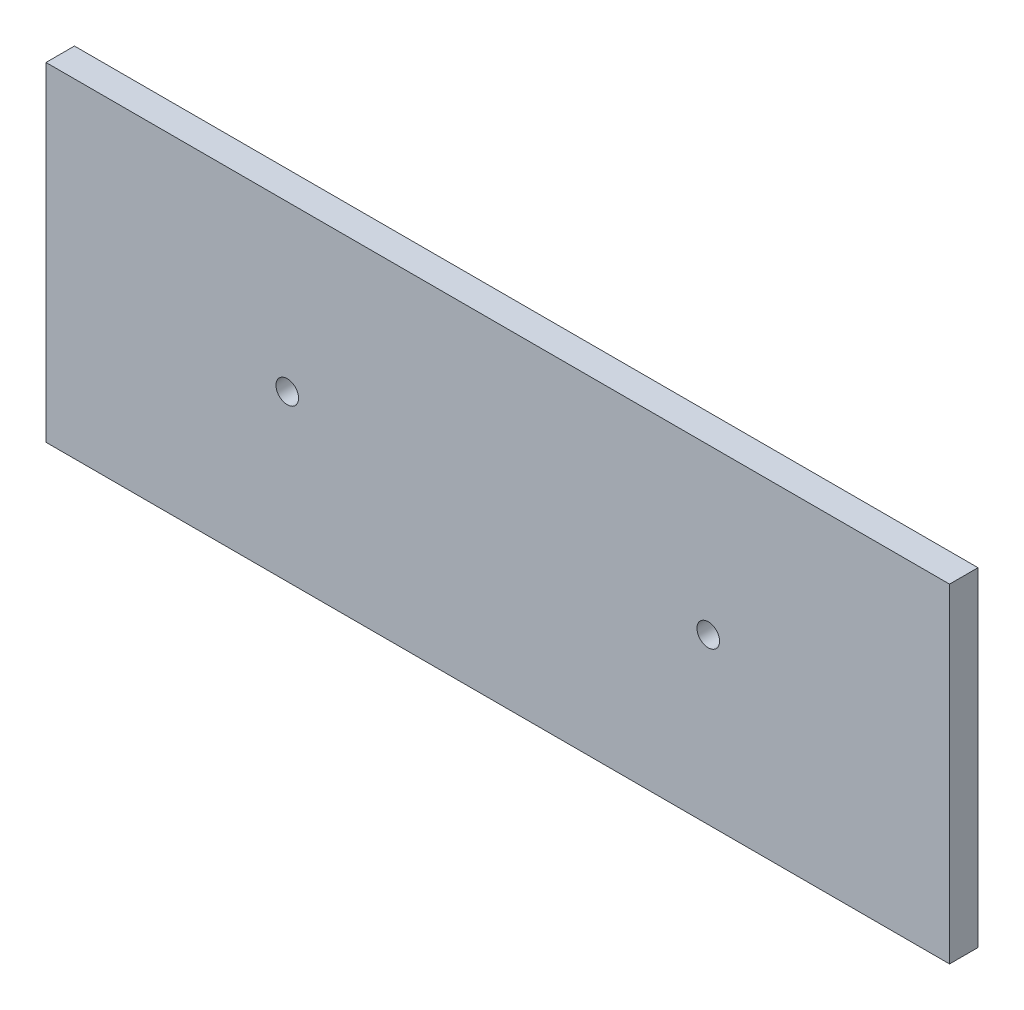
SolidWorks part; units mm, degrees
material "AISI 4130 Steel, annealed at 865C"
ref_plane "Front Plane" through (0, 0, 0) normal (0, 0, 1) x (1, 0, 0)
ref_plane "Top Plane" through (0, 0, 0) normal (0, 1, 0) x (1, 0, 0)
ref_plane "Right Plane" through (0, 0, 0) normal (1, 0, 0) x (0, 0, -1)
sketch "Model" plane through (0, 0, 0) normal (0, 0, 1) x (1, 0, 0)
  line L0 (155.4087, -23.9371) -> (91.9087, -23.9371)
  line L1 (155.4087, -11.2371) -> (91.9087, -11.2371)
  line L3 (91.9087, -29.1468) -> (155.4087, -29.1468)
  line L4 (91.9087, -29.1468) -> (91.9087, -6.0273)
  line L5 (91.9087, -6.0273) -> (155.4087, -6.0273)
  line L6 (155.4087, -29.1468) -> (155.4087, -6.0273)
  circle A0 centre (138.4521, -17.5871) radius 0.7937
  circle A1 centre (108.8653, -17.5871) radius 0.7937
  point P11 (108.8653, -17.5871)
  point P12 (138.4521, -17.5871)
  point P16 (91.9087, -17.5871)
  dimension "D1" = 63.5
extrude "Boss-Extrude1" add sketch "Model" along normal blind 2 contours L0 L6 L1 L4 A1 A0 | L1 L6 L5 L4 | L3 L6 L0 L4
